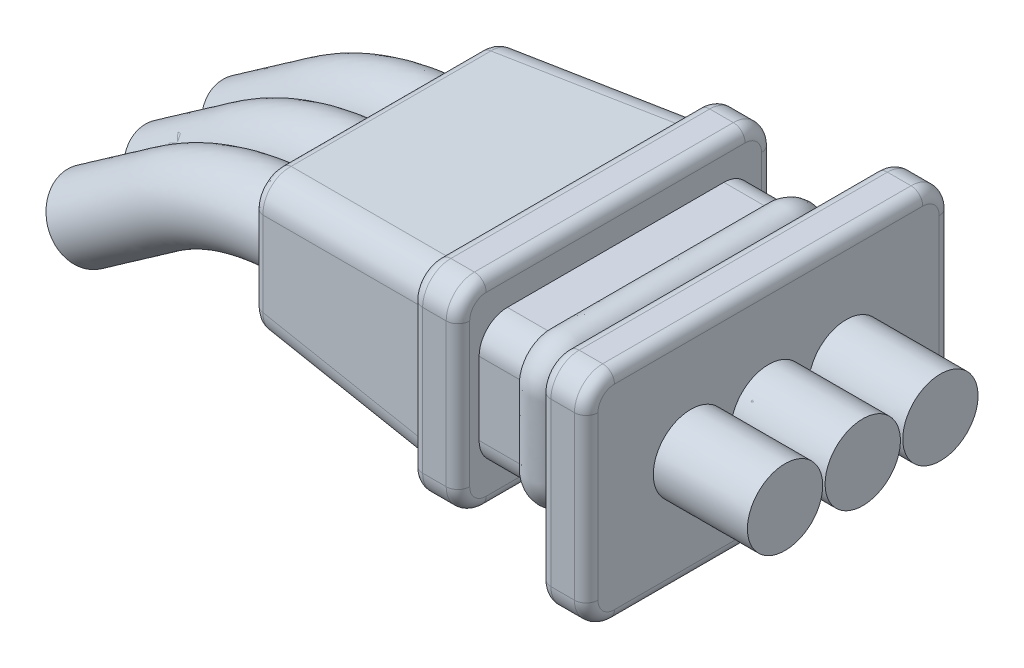
SolidWorks part; units mm, degrees
material "Rubber"
ref_plane "Front Plane" through (0, 0, 0) normal (0, 0, 1) x (1, 0, 0)
ref_plane "Top Plane" through (0, 0, 0) normal (0, 1, 0) x (1, 0, 0)
ref_plane "Right Plane" through (0, 0, 0) normal (1, 0, 0) x (0, 0, -1)
sketch "Sketch1" plane through (0, 0, 0) normal (1, 0, 0) x (0, 0, -1)
  line L1 (-3.875, 2.325) -> (3.875, 2.325)
  line L2 (-3.875, 2.325) -> (-3.875, -2.325)
  line L3 (-3.875, -2.325) -> (3.875, -2.325)
  line L4 (3.875, 2.325) -> (3.875, -2.325)
  line L5 (-3.875, 2.325) -> (3.875, -2.325) construction
  line L6 (-3.875, -2.325) -> (3.875, 2.325) construction
  point P0 (0, 0)
  dimension "D1" = 7.75
  dimension "D2" = 4.65
extrude "Boss-Extrude1" add sketch "Sketch1" along normal blind 1
sketch "Sketch2" plane through (0, 0, 0) normal (-1, 0, 0) x (0, 0, 1)
  line L1 (2.9, -1.375) -> (-2.9, -1.375)
  line L2 (2.9, -1.375) -> (2.9, 1.375)
  line L3 (2.9, 1.375) -> (-2.9, 1.375)
  line L4 (-2.9, -1.375) -> (-2.9, 1.375)
  line L5 (2.9, -1.375) -> (-2.9, 1.375) construction
  line L6 (2.9, 1.375) -> (-2.9, -1.375) construction
  point P0 (0, 0)
  dimension "D1" = 5.8
  dimension "D2" = 2.75
extrude "Boss-Extrude2" add sketch "Sketch2" along normal blind 2.25
sketch "Sketch3" plane through (-2.25, 0, 0) normal (-1, 0, 0) x (0, 0, 1)
  line L1 (3.35, -2.125) -> (-3.35, -2.125)
  line L2 (3.35, -2.125) -> (3.35, 2.125)
  line L3 (3.35, 2.125) -> (-3.35, 2.125)
  line L4 (-3.35, -2.125) -> (-3.35, 2.125)
  line L5 (3.35, -2.125) -> (-3.35, 2.125) construction
  line L6 (3.35, 2.125) -> (-3.35, -2.125) construction
  point P0 (0, 0)
  dimension "D1" = 6.7
  dimension "D2" = 4.25
extrude "Boss-Extrude3" add sketch "Sketch3" along normal blind 1
sketch "Sketch4" plane through (-3.25, 0, 0) normal (-1, 0, 0) x (0, 0, 1)
  line L1 (3.05, -1.825) -> (-3.05, -1.825)
  line L2 (3.05, -1.825) -> (3.05, 1.825)
  line L3 (3.05, 1.825) -> (-3.05, 1.825)
  line L4 (-3.05, -1.825) -> (-3.05, 1.825)
  line L5 (3.05, -1.825) -> (-3.05, 1.825) construction
  line L6 (3.05, 1.825) -> (-3.05, -1.825) construction
  point P0 (0, 0)
  dimension "D1" = 6.1
  dimension "D2" = 3.65
extrude "Boss-Extrude4" add sketch "Sketch4" along normal blind 4 draft 5
fillet "Fillet1" radius 0.6 16 edges at (-1.125, -1.375, -2.9) (-1.125, 1.375, -2.9) (-1.125, -1.375, 2.9) (0.5, 2.325, -3.875) (0.5, -2.325, -3.875) (0.5, -2.325, 3.875) (-2.75, 2.125, -3.35) (-2.75, -2.125, -3.35) (-5.25, -1.65, -2.875) (-5.25, -1.65, 2.875) (-5.25, 1.65, -2.875) (-2.75, -2.125, 3.35) (0.5, 2.325, 3.875) (-1.125, 1.375, 2.9) (-5.25, 1.65, 2.875) (-2.75, 2.125, 3.35)
sketch "Sketch7" plane through (0, 0, 0) normal (-1, 0, 0) x (0, 0, 1)
  line L0 (-2.3, -1.375) -> (2.3, -1.375) construction
  line L1 (-2.9, 0.775) -> (-2.9, -0.775) construction
  line L2 (2.9, -0.775) -> (2.9, 0.775) construction
  line L3 (2.3, 1.375) -> (-2.3, 1.375) construction
  line L4 (-2.3, -1.375) -> (2.3, -1.375)
  line L5 (-2.9, 0.775) -> (-2.9, -0.775)
  line L6 (2.9, -0.775) -> (2.9, 0.775)
  line L7 (2.3, 1.375) -> (-2.3, 1.375)
  arc A0 (-2.9, -0.775) -> (-2.3, -1.375) centre (-2.3, -0.775) ccw construction
  arc A1 (-2.3, 1.375) -> (-2.9, 0.775) centre (-2.3, 0.775) ccw construction
  arc A2 (2.3, -1.375) -> (2.9, -0.775) centre (2.3, -0.775) ccw construction
  arc A3 (2.9, 0.775) -> (2.3, 1.375) centre (2.3, 0.775) ccw construction
  arc A4 (-2.9, -0.775) -> (-2.3, -1.375) centre (-2.3, -0.775) ccw
  arc A5 (-2.3, 1.375) -> (-2.9, 0.775) centre (-2.3, 0.775) ccw
  arc A6 (2.3, -1.375) -> (2.9, -0.775) centre (2.3, -0.775) ccw
  arc A7 (2.9, 0.775) -> (2.3, 1.375) centre (2.3, 0.775) ccw
sketch "Sketch5" plane through (0, 0, 0) normal (0, 1, 0) x (1, 0, 0)
  line L1 (-0.625, 2.9) -> (-1, 2.6835) construction
  line L3 (-1, 2.6835) -> (-1.375, 2.9) construction
  line L5 (-2.25, 2.9) -> (0, 2.9) construction
  line L6 (-2.25, -2.75) -> (-2.25, 2.75) construction
  line L7 (-0.625, 2.9) -> (-1.375, 2.9)
  arc A0 (-1.375, 2.9) -> (-0.625, 2.9) centre (-1, 2.6835) cw
  dimension "D1" = 0.75
  dimension "D2" = 0.875
  dimension "D3" = 120
sweep "Sweep2" add profiles "Sketch5" path "Sketch7"
fillet "Fillet2" radius 0.25 40 edges at (1, -2.1493, 3.6993) (1, 0, 3.875) (1, 2.1493, 3.6993) (1, 2.325, 0) (1, 2.1493, -3.6993) (1, 0, -3.875) (1, -2.1493, -3.6993) (0, -2.1493, 3.6993) (0, 0, 3.875) (0, 2.1493, 3.6993) (0, 2.325, 0) (0, 2.1493, -3.6993) (0, 0, -3.875) (0, -2.1493, -3.6993) (1, -2.325, 0) (0, -2.325, 0) (-7.25, -1.3003, -2.5253) (-7.25, 0, -2.7) (-7.25, 1.3003, -2.5253) (-7.25, 1.475, 0) (-7.25, 1.3003, 2.5253) (-7.25, 0, 2.7) (-7.25, -1.3003, 2.5253) (-3.25, -1.9493, -3.1743) (-3.25, 0, -3.35) (-3.25, 1.9493, -3.1743) (-3.25, 2.125, 0) (-3.25, 1.9493, 3.1743) (-3.25, 0, 3.35) (-3.25, -1.9493, 3.1743) (-2.25, -1.9493, -3.1743) (-2.25, 0, -3.35) (-2.25, 1.9493, -3.1743) (-2.25, 2.125, 0) (-2.25, 1.9493, 3.1743) (-2.25, 0, 3.35) (-2.25, -1.9493, 3.1743) (-7.25, -1.475, 0) (-3.25, -2.125, 0) (-2.25, -2.125, 0)
sketch "Sketch15" plane through (-7.25, 0, 0) normal (-1, 0, 0) x (0, 0, 1)
  line L0 (0, 0) -> (1.65, 0) construction
  line L1 (0, 0) -> (-1.65, 0) construction
  line L2 (-0.8547, 0.25) -> (-0.7953, 0.25)
  line L3 (-0.8547, -0.25) -> (-0.7953, -0.25)
  line L4 (0.7953, -0.25) -> (0.8547, -0.25)
  line L5 (0.7953, 0.25) -> (0.8547, 0.25)
  arc A0 (0.7485, 0.2824) -> (-0.7485, 0.2824) centre (0, 0) ccw
  arc A1 (0.9015, -0.2824) -> (0.9015, 0.2824) centre (1.65, 0) ccw
  arc A2 (-0.9015, 0.2824) -> (-0.9015, -0.2824) centre (-1.65, 0) ccw
  arc A3 (-0.7485, -0.2824) -> (0.7485, -0.2824) centre (0, 0) ccw
  arc A4 (0.8547, -0.25) -> (0.9015, -0.2824) centre (0.8547, -0.3) cw
  arc A5 (0.7485, -0.2824) -> (0.7953, -0.25) centre (0.7953, -0.3) cw
  arc A6 (0.7485, 0.2824) -> (0.7953, 0.25) centre (0.7953, 0.3) ccw
  arc A7 (0.8547, 0.25) -> (0.9015, 0.2824) centre (0.8547, 0.3) ccw
  arc A8 (-0.7953, -0.25) -> (-0.7485, -0.2824) centre (-0.7953, -0.3) cw
  arc A9 (-0.8547, -0.25) -> (-0.9015, -0.2824) centre (-0.8547, -0.3) ccw
  arc A10 (-0.7953, 0.25) -> (-0.7485, 0.2824) centre (-0.7953, 0.3) ccw
  arc A11 (-0.8547, 0.25) -> (-0.9015, 0.2824) centre (-0.8547, 0.3) cw
  point P20 (0.7599, -0.25)
  point P23 (0.7599, 0.25)
  point P28 (-0.7599, -0.25)
  dimension "D1" = 1.6
  dimension "D7" = 0.05
  dimension "D3" = 1.65
  dimension "D5" = 1.65
  dimension "D6" = 0.5
  dimension "D2" = 2
  dimension "D4" = 2
extrude "Cut-Extrude6" cut sketch "Sketch15" against normal through all
sketch "Sketch10" plane through (0, 0, 0) normal (0, 0, 1) x (1, 0, 0)
  line L0 (1, 0) -> (-7.2735, 0)
  line L1 (1, 1.725) -> (1, -1.725) construction
  line L2 (-7.25, -0.8973) -> (-7.25, 0.8973) construction
  line L3 (-10.1414, -0.9042) -> (-11.7797, -2.0514)
  line L4 (1, 0) -> (3, 0)
  arc A0 (-7.2735, 0) -> (-10.1414, -0.9042) centre (-7.2735, -5) ccw
  point P10 (-8.85, 0)
  dimension "D3" = 5
  dimension "D1" = 1.6
  dimension "D2" = 145
  dimension "D4" = 2
  dimension "D5" = 2
sweep "Sweep3" add path "Sketch10" circular profile diameter 1.6 parameters "D3"=1.6
pattern_linear "LPattern1" count 2 spacing 1.65 along (0, 0, 1) count 2 spacing 1.65 along (0, 0, -1) of "Sweep3"
